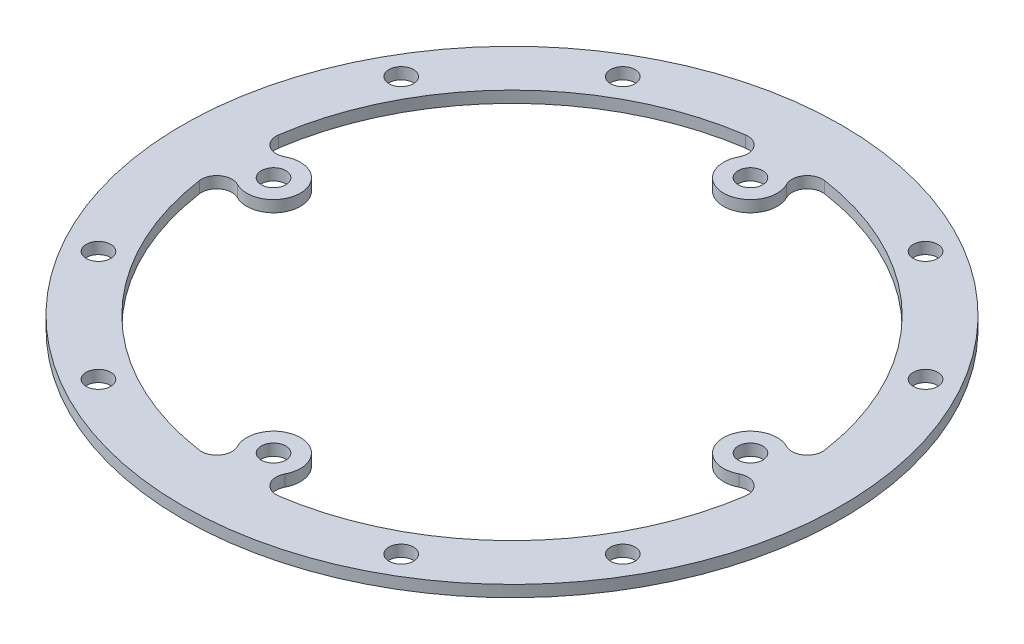
SolidWorks part; units mm, degrees
material "Thornel Mat VMA"
ref_plane "Front Plane" through (0, 0, 0) normal (0, 0, 1) x (1, 0, 0)
ref_plane "Top Plane" through (0, 0, 0) normal (0, 1, 0) x (1, 0, 0)
ref_plane "Right Plane" through (0, 0, 0) normal (1, 0, 0) x (0, 0, -1)
sketch "Sketch1" plane through (0, 0, 0) normal (0, 1, 0) x (1, 0, 0)
  circle A0 centre (0, 0) radius 43
  dimension "D1" = 86
extrude "Boss-Extrude1" add sketch "Sketch1" along normal mid plane 1.5
hole_wizard "Ø3.2 (3.2) Diameter Hole1" positions "Sketch3" profile "Sketch2" hole size "Ø3.2" standard "ANSI Metric" end condition through all
sketch "Sketch3" plane through (0, 0.75, 0) normal (0, 1, 0) x (1, 0, 0)
  line L0 (0, 0) -> (-43, 0) construction
  line L3 (0, 0) -> (-37.2391, 21.5) construction
  line L6 (0, 0) -> (-37.2391, -21.5) construction
  circle A0 centre (0, 0) radius 43 construction
  point P25 (-34.208, 19.75)
  point P27 (-34.208, -19.75)
  point P30 (-31.1127, 0)
  point P37 (19.75, 34.208)
  point P38 (-19.75, 34.208)
  point P39 (0, 31.1127)
  point P40 (34.208, -19.75)
  point P41 (34.208, 19.75)
  point P42 (31.1127, 0)
  point P43 (-19.75, -34.208)
  point P44 (19.75, -34.208)
  point P45 (0, -31.1127)
  point P46 (0, 0)
  dimension "D1" = 30
  dimension "D2" = 30
  dimension "D3" = 39.5
  dimension "D4" = 39.5
  dimension "D6" = 44
  dimension "D5" = 4
sketch "Sketch2" plane through (-34.208, 0.75, -19.75) normal (1, 0, 0) x (0, 0, 1)
  line L0 (0, 0) -> (0, 1.5)
  line L1 (0, 1.5) -> (1.6, 1.5)
  line L2 (1.6, 1.5) -> (1.6, 0)
  line L5 (1.6, 0) -> (0, 0)
  line L11 (0, -6.35) -> (0, 107.95) construction
  dimension "Thru Hole Dia." = 3.2
  dimension "Thru Hole Depth" = 1.5
sketch "Sketch4" plane through (0, 0.75, 0) normal (0, 1, 0) x (1, 0, 0)
  arc A0 (-35.6271, -5.168) -> (-5.168, -35.6271) centre (0, 0) ccw
  circle A1 centre (0, 0) radius 43 construction
  arc A2 (-32.726, -3.106) -> (-32.726, 3.106) centre (-31.1127, 0) ccw
  arc A3 (-35.6271, 5.168) -> (-32.726, 3.106) centre (-33.6478, 4.8809) ccw
  arc A4 (-32.726, -3.106) -> (-35.6271, -5.168) centre (-33.6478, -4.8809) ccw
  arc A5 (-3.106, 32.726) -> (3.106, 32.726) centre (0, 31.1127) ccw
  arc A6 (5.168, 35.6271) -> (3.106, 32.726) centre (4.8809, 33.6478) ccw
  arc A7 (-3.106, 32.726) -> (-5.168, 35.6271) centre (-4.8809, 33.6478) ccw
  arc A8 (32.726, 3.106) -> (32.726, -3.106) centre (31.1127, 0) ccw
  arc A9 (35.6271, -5.168) -> (32.726, -3.106) centre (33.6478, -4.8809) ccw
  arc A10 (32.726, 3.106) -> (35.6271, 5.168) centre (33.6478, 4.8809) ccw
  arc A11 (3.106, -32.726) -> (-3.106, -32.726) centre (0, -31.1127) ccw
  arc A12 (-5.168, -35.6271) -> (-3.106, -32.726) centre (-4.8809, -33.6478) ccw
  arc A13 (3.106, -32.726) -> (5.168, -35.6271) centre (4.8809, -33.6478) ccw
  arc A14 (-5.168, 35.6271) -> (-35.6271, 5.168) centre (0, 0) ccw
  arc A15 (35.6271, 5.168) -> (5.168, 35.6271) centre (0, 0) ccw
  arc A16 (5.168, -35.6271) -> (35.6271, -5.168) centre (0, 0) ccw
  point P36 (0, 0)
  dimension "D1" = 7
  dimension "D2" = 4
  dimension "D3" = 7
  dimension "D4" = 4
extrude "Cut-Extrude1" cut sketch "Sketch4" against normal through all
